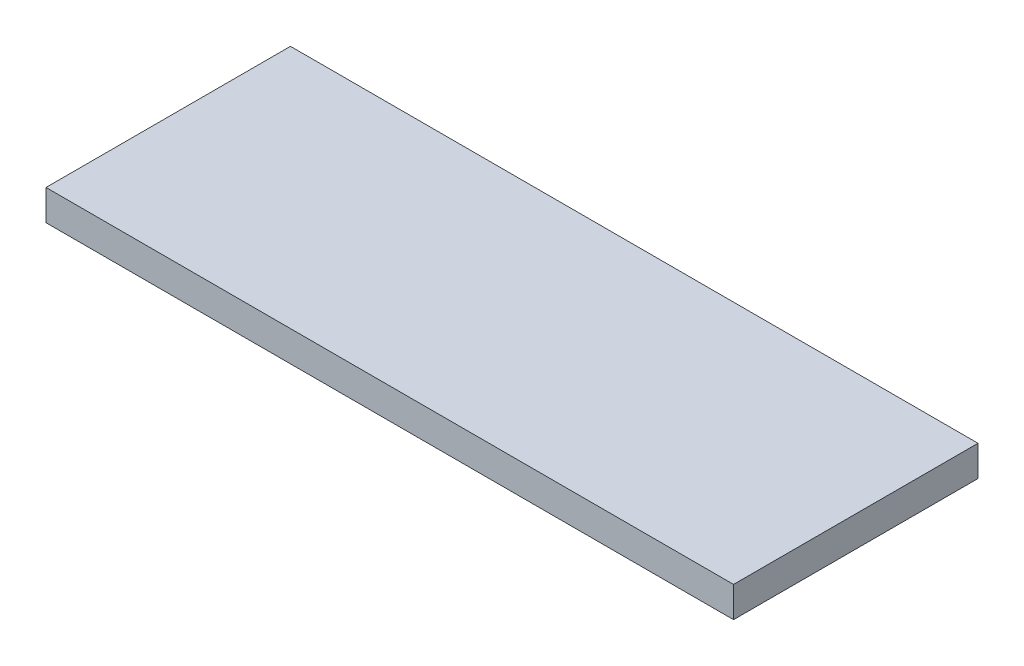
SolidWorks part; units mm, degrees
ref_plane "Front Plane" through (0, 0, 0) normal (0, 0, 1) x (1, 0, 0)
ref_plane "Top Plane" through (0, 0, 0) normal (0, 1, 0) x (1, 0, 0)
ref_plane "Right Plane" through (0, 0, 0) normal (1, 0, 0) x (0, 0, -1)
sketch "Sketch1" plane through (0, 0, 0) normal (0, 1, 0) x (1, 0, 0)
  line L1 (-225, -80) -> (225, -80)
  line L2 (-225, -80) -> (-225, 80)
  line L3 (-225, 80) -> (225, 80)
  line L4 (225, -80) -> (225, 80)
  line L5 (-225, -80) -> (225, 80) construction
  line L6 (-225, 80) -> (225, -80) construction
  point P0 (0, 0)
  dimension "D1" = 450
  dimension "D2" = 160
extrude "Boss-Extrude1" add sketch "Sketch1" along normal blind 20
